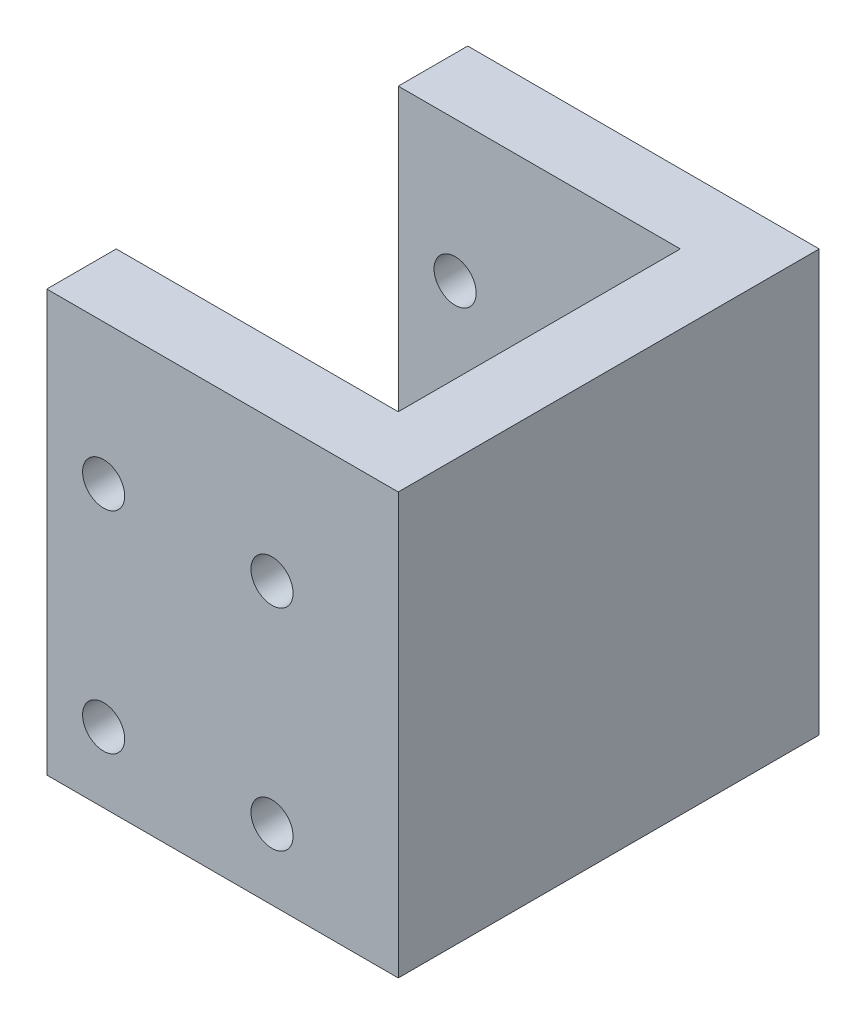
SolidWorks part; units mm, degrees
ref_plane "Front Plane" through (0, 0, 0) normal (0, 0, 1) x (1, 0, 0)
ref_plane "Top Plane" through (0, 0, 0) normal (0, 1, 0) x (1, 0, 0)
ref_plane "Right Plane" through (0, 0, 0) normal (1, 0, 0) x (0, 0, -1)
sketch "Sketch2" plane through (0, -470, 0) normal (0, -1, 0) x (1, 0, 0)
  line L0 (-400.3658, -355.2) -> (-380.3658, -355.2) construction
  line L1 (-400.4158, -350.2) -> (-380.3158, -350.2)
  line L3 (-400.4158, -380.2) -> (-380.3158, -380.2)
  line L4 (-380.3658, -375.2) -> (-400.3658, -375.2) construction
  line L5 (-380.3658, -355.2) -> (-380.3658, -375.2) construction
  line L6 (-400.3658, -375.2) -> (-400.3658, -355.2) construction
  line L7 (-380.3158, -355.15) -> (-380.3158, -375.25)
  line L12 (-375.3658, -350.2) -> (-375.3658, -380.2)
  line L16 (-400.4158, -355.15) -> (-400.4158, -375.25)
  line L17 (-400.4158, -375.25) -> (-380.3158, -375.25)
  line L18 (-380.3158, -375.25) -> (-380.3158, -355.15)
  line L19 (-380.3158, -355.15) -> (-400.4158, -355.15)
  line L22 (-375.3658, -350.2) -> (-375.3658, -380.2)
  line L25 (-400.4158, -355.15) -> (-400.4158, -375.25)
  line L28 (-400.4158, -350.2) -> (-400.4158, -355.15)
  line L29 (-400.4158, -375.25) -> (-400.4158, -380.2)
  line L30 (-380.3158, -380.2) -> (-375.3658, -380.2)
  line L31 (-380.3158, -350.2) -> (-375.3658, -350.2)
  dimension "D2" = 4.95
  dimension "D3" = 4.95
  dimension "D5" = 4.95
  dimension "D1" = 0.05
  dimension "D6" = 0.05
  dimension "D7" = 0.05
  dimension "D8" = 0.05
extrude "Extrude1" add sketch "Sketch2" against normal blind 30
sketch "Sketch3" plane through (0, 0, -350.2) normal (0, 0, 1) x (1, 0, 0)
  circle A0 centre (-384.3658, -465) radius 1.5 construction
  circle A1 centre (-396.3658, -465) radius 1.5 construction
  circle A2 centre (-384.3658, -450) radius 1.5 construction
  circle A3 centre (-396.3658, -450) radius 1.5 construction
  circle A4 centre (-384.3658, -465) radius 1.5
  circle A5 centre (-396.3658, -465) radius 1.5
  circle A6 centre (-384.3658, -450) radius 1.5
  circle A7 centre (-396.3658, -450) radius 1.5
extrude "Cut-Extrude1" cut sketch "Sketch3" against normal blind 30
